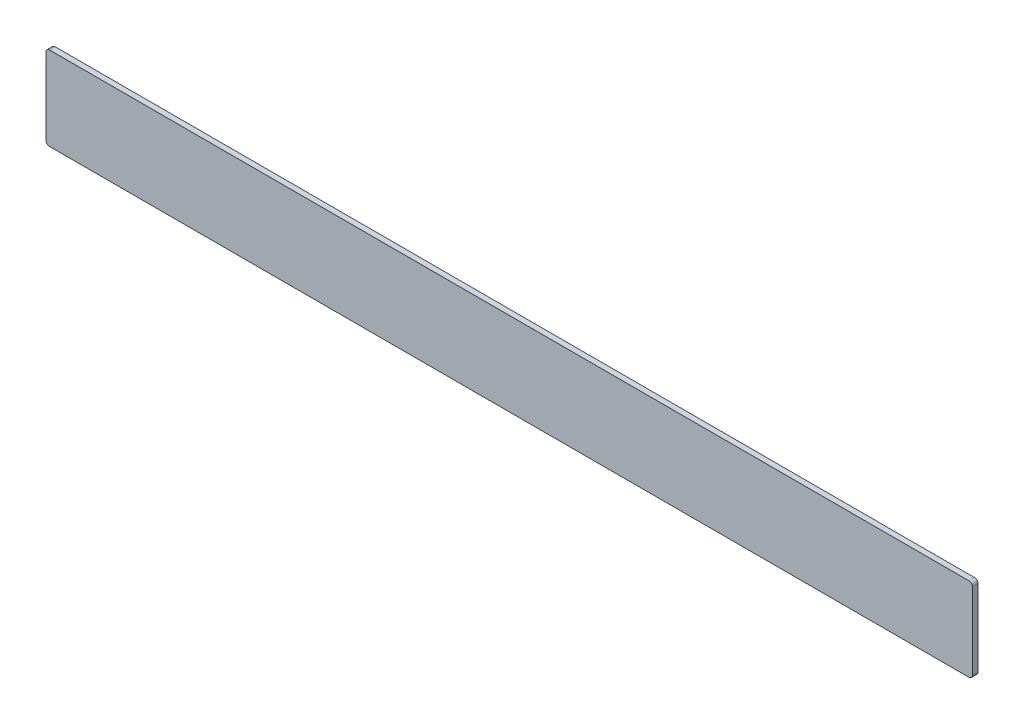
SolidWorks part; units mm, degrees
material "Plain Carbon Steel"
ref_plane "Front Plane" through (0, 0, 0) normal (0, 0, 1) x (1, 0, 0)
ref_plane "Top Plane" through (0, 0, 0) normal (0, 1, 0) x (1, 0, 0)
ref_plane "Right Plane" through (0, 0, 0) normal (1, 0, 0) x (0, 0, -1)
sketch "Sketch1" plane through (0, 0, 0) normal (0, 0, 1) x (1, 0, 0)
  line L1 (-665, -60) -> (665, -60)
  line L2 (-665, -60) -> (-665, 60)
  line L3 (-665, 60) -> (665, 60)
  line L4 (665, -60) -> (665, 60)
  line L5 (-665, -60) -> (665, 60) construction
  line L6 (-665, 60) -> (665, -60) construction
  point P0 (0, 0)
  dimension "D1" = 1330
  dimension "D2" = 120
extrude "Boss-Extrude1" add sketch "Sketch1" along normal mid plane 8
fillet "Fillet1" radius 5 4 edges at (665, -60, 0) (665, 60, 0) (-665, -60, 0) (-665, 60, 0)
